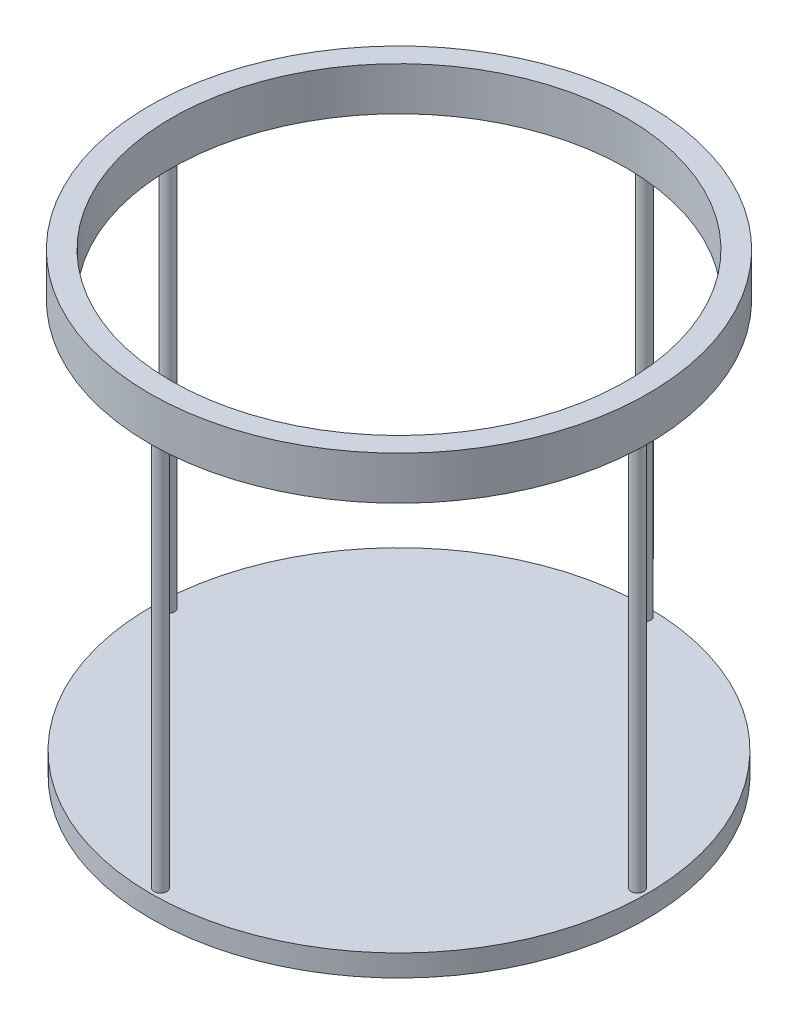
SolidWorks part; units mm, degrees
ref_plane "Front Plane" through (0, 0, 0) normal (0, 0, 1) x (1, 0, 0)
ref_plane "Top Plane" through (0, 0, 0) normal (0, 1, 0) x (1, 0, 0)
ref_plane "Right Plane" through (0, 0, 0) normal (1, 0, 0) x (0, 0, -1)
sketch "Sketch1" plane through (0, 0, 0) normal (0, 1, 0) x (1, 0, 0)
  circle A0 centre (0, 0) radius 52.5
  circle A1 centre (0, 0) radius 57.5
  dimension "D1" = 105
  dimension "D2" = 115
extrude "Boss-Extrude1" add sketch "Sketch1" along normal blind 10
sketch "Sketch2" plane through (0, 0, 0) normal (0, -1, 0) x (1, 0, 0)
  circle A0 centre (0, 55) radius 1.45
  circle A1 centre (1.5782, -55) radius 1.45
  circle A2 centre (55, 0) radius 1.45
  circle A3 centre (-55, -1.7603) radius 1.45
  circle A4 centre (0, 0) radius 52.5 construction
  dimension "D1" = 2.9
  dimension "D2" = 2.9
  dimension "D3" = 2.9
  dimension "D4" = 2.9
  dimension "D5" = 55
  dimension "D6" = 55
  dimension "D7" = 55
  dimension "D8" = 55
extrude "Boss-Extrude2" add sketch "Sketch2" along normal blind 90
sketch "Sketch4" plane through (0, -90, 0) normal (0, -1, 0) x (-1, 0, 0)
  circle A0 centre (0, 0) radius 57.2277
extrude "Boss-Extrude3" add sketch "Sketch4" along normal blind 5
